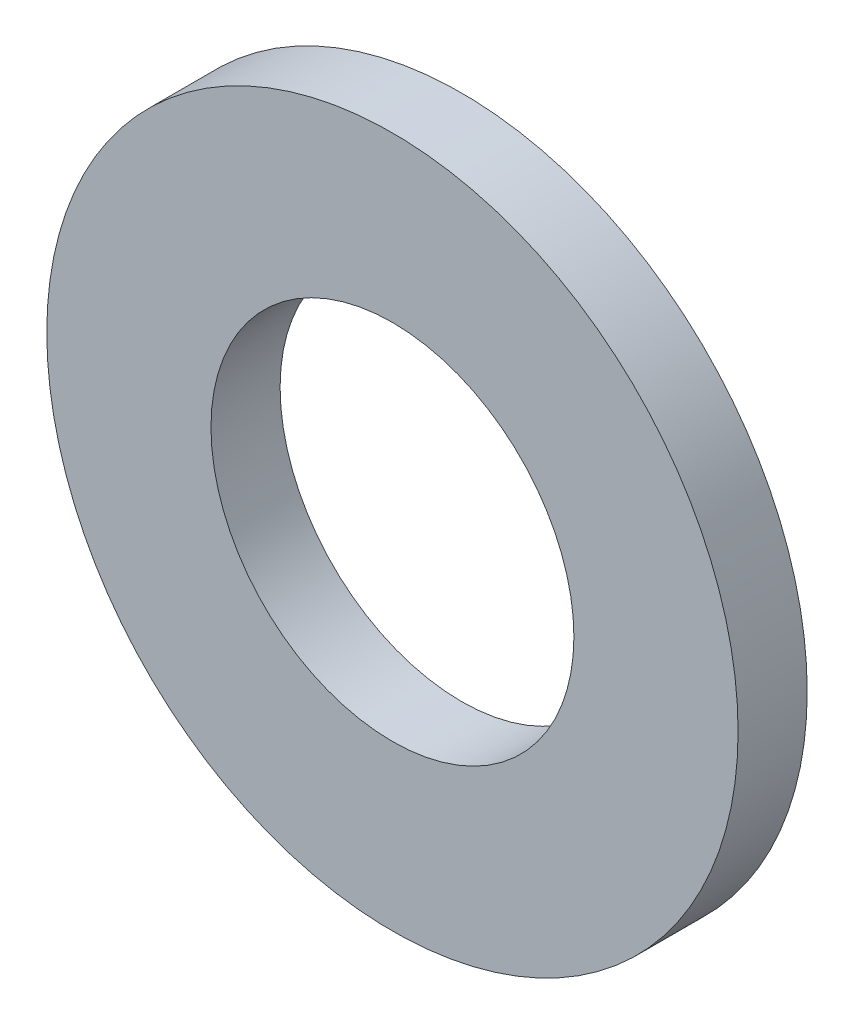
SolidWorks part; units mm, degrees
material "Polyetheretherketone (PEEK)"
ref_plane "Front Plane" through (0, 0, 0) normal (0, 0, 1) x (1, 0, 0)
ref_plane "Top Plane" through (0, 0, 0) normal (0, 1, 0) x (1, 0, 0)
ref_plane "Right Plane" through (0, 0, 0) normal (1, 0, 0) x (0, 0, -1)
sketch "Sketch1" plane through (0, 0, 0) normal (0, 0, 1) x (1, 0, 0)
  circle A0 centre (0, 0) radius 10
  dimension "D1" = 20
extrude "Boss-Extrude1" add sketch "Sketch1" along normal blind 2
sketch "Sketch2" plane through (0, 0, 0) normal (0, 0, 1) x (1, 0, 0)
  circle A0 centre (0, 0) radius 5.25
  dimension "D1" = 10.5
extrude "Cut-Extrude2" cut sketch "Sketch2" along normal through all
